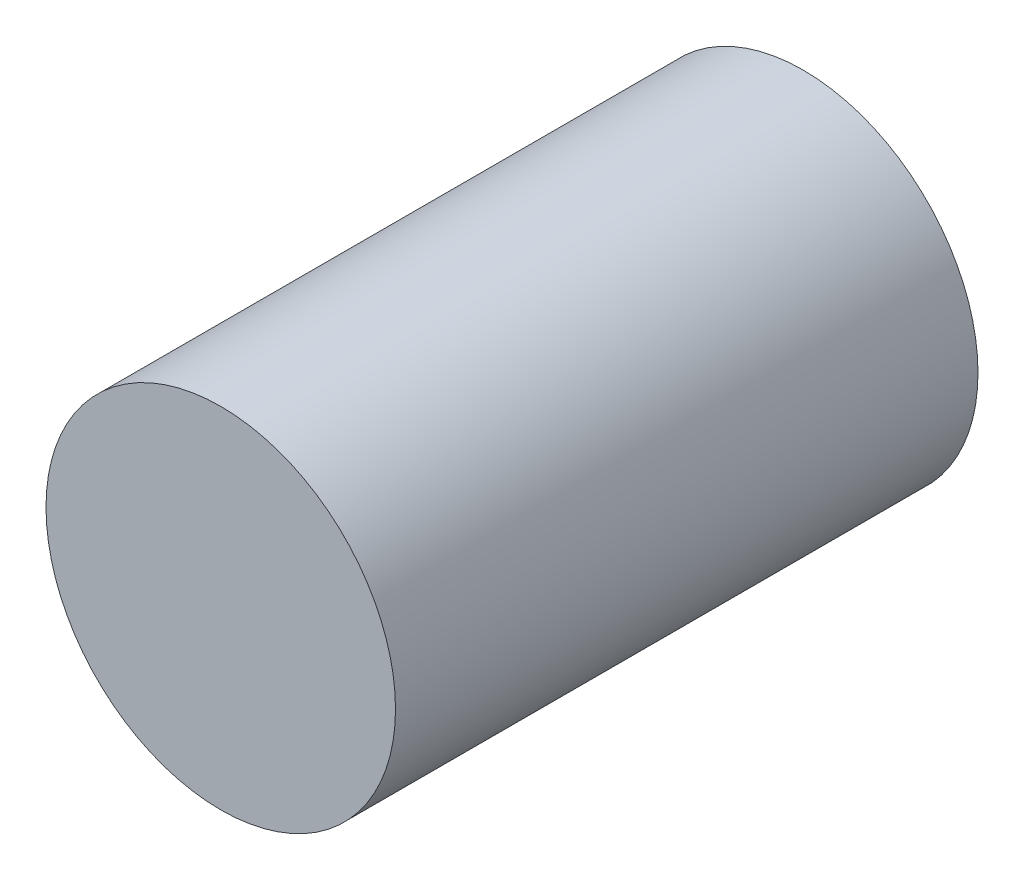
SolidWorks part; units mm, degrees
ref_plane "Front Plane" through (0, 0, 0) normal (0, 0, 1) x (1, 0, 0)
ref_plane "Top Plane" through (0, 0, 0) normal (0, 1, 0) x (1, 0, 0)
ref_plane "Right Plane" through (0, 0, 0) normal (1, 0, 0) x (0, 0, -1)
sketch "Sketch1" plane through (0, 0, 0) normal (0, 0, 1) x (1, 0, 0)
  circle A0 centre (0, 0) radius 13.5
  dimension "D1" = 27
extrude "Boss-Extrude1" add sketch "Sketch1" along normal blind 45
